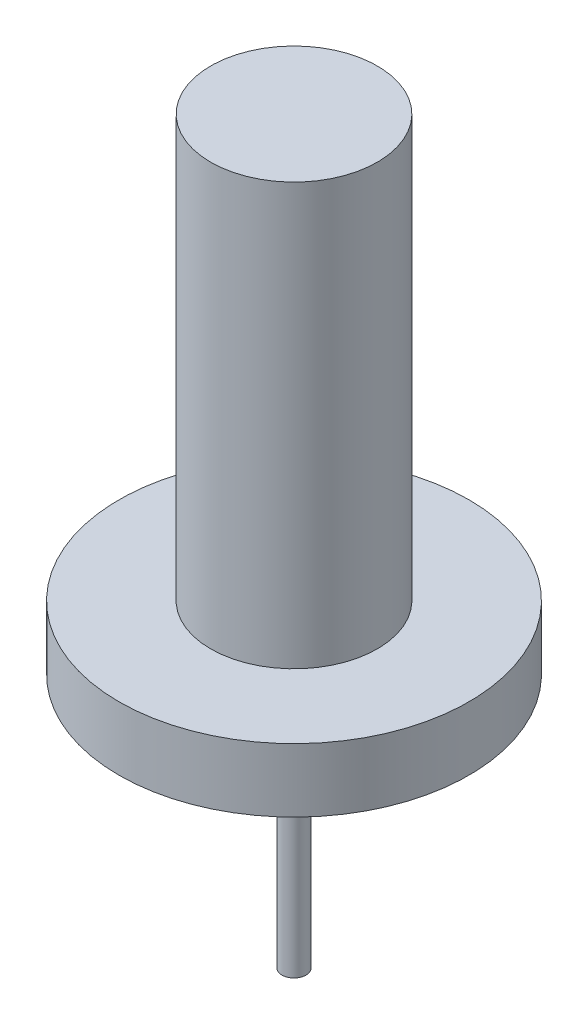
SolidWorks part; units mm, degrees
ref_plane "Front Plane" through (0, 0, 0) normal (0, 0, 1) x (1, 0, 0)
ref_plane "Top Plane" through (0, 0, 0) normal (0, 1, 0) x (1, 0, 0)
ref_plane "Right Plane" through (0, 0, 0) normal (1, 0, 0) x (0, 0, -1)
sketch "Sketch1" plane through (0, 0, 0) normal (0, 1, 0) x (1, 0, 0)
  circle A0 centre (0, 0) radius 34.925
  dimension "D1" = 69.85
extrude "Extrude1" add sketch "Sketch1" along normal blind 12.7
sketch "Sketch2" plane through (0, 12.7, 0) normal (0, 1, 0) x (1, 0, 0)
  circle A0 centre (0, 0) radius 16.637
  dimension "D1" = 33.274
extrude "Extrude2" add sketch "Sketch2" along normal blind 84.1248
sketch "Sketch3" plane through (0, 0, 0) normal (0, -1, 0) x (1, 0, 0)
  circle A0 centre (0, 0) radius 2.4079
extrude "Extrude3" add sketch "Sketch3" along normal blind 50.8
